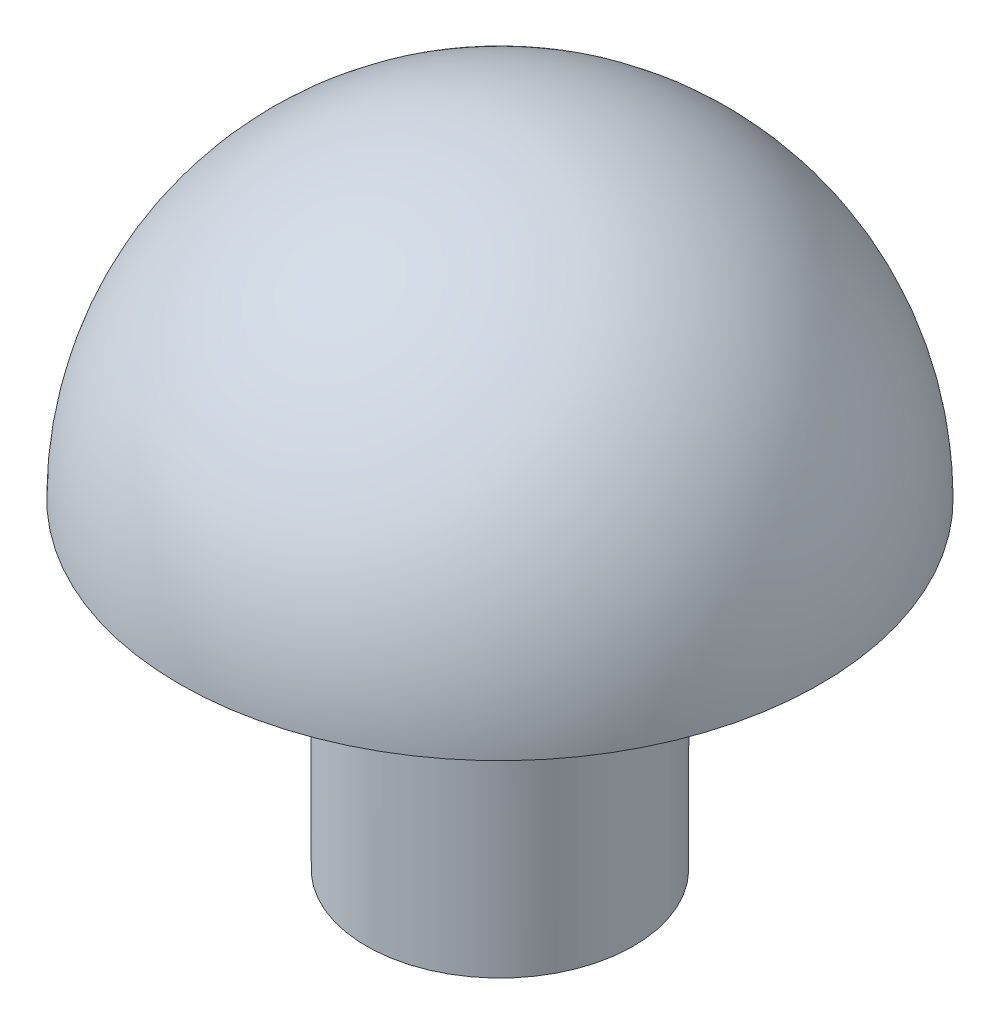
SolidWorks part; units mm, degrees
ref_plane "Front Plane" through (0, 0, 0) normal (0, 0, 1) x (1, 0, 0)
ref_plane "Top Plane" through (0, 0, 0) normal (0, 1, 0) x (1, 0, 0)
ref_plane "Right Plane" through (0, 0, 0) normal (1, 0, 0) x (0, 0, -1)
sketch "Sketch1" plane through (0, 0, 0) normal (0, 1, 0) x (1, 0, 0)
  circle A0 centre (0, 0) radius 2.5
  dimension "D1" = 5
extrude "Boss-Extrude1" add sketch "Sketch1" along normal blind 3
sketch "Sketch2" plane through (0, 3, 0) normal (0, 1, 0) x (1, 0, 0)
  line L0 (0, -6) -> (0, 6)
  arc A0 (0, -6) -> (0, 6) centre (0, 0) ccw
  circle A1 centre (0, 0) radius 2.5 construction
  dimension "D1" = 6
  dimension "D3" = 6
  dimension "D4" = 0
revolve "Revolve1" add sketch "Sketch2" angle 180 about L0
sketch "Sketch3" plane through (0, 0, 0) normal (0, -1, 0) x (1, 0, 0)
  circle A0 centre (0, 0) radius 2.5
extrude "Boss-Extrude2" add sketch "Sketch3" along normal blind 3
